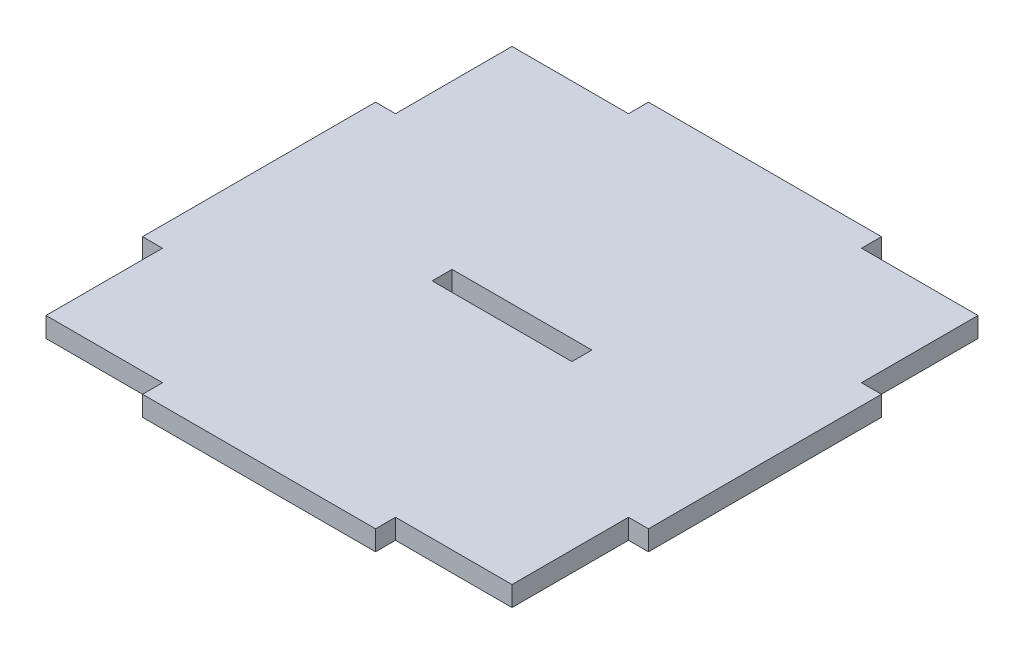
SolidWorks part; units mm, degrees
ref_plane "Front Plane" through (0, 0, 0) normal (0, 0, 1) x (1, 0, 0)
ref_plane "Top Plane" through (0, 0, 0) normal (0, 1, 0) x (1, 0, 0)
ref_plane "Right Plane" through (0, 0, 0) normal (1, 0, 0) x (0, 0, -1)
sketch "Sketch1" plane through (0, 0, 0) normal (0, 1, 0) x (1, 0, 0)
  line L0 (0, 35) -> (0, -35) construction
  line L1 (-35, -35) -> (-17.5, -35)
  line L2 (-35, -35) -> (-35, -17.5)
  line L3 (-35, 35) -> (-17.5, 35)
  line L4 (35, -35) -> (35, -17.5)
  line L5 (-35, -35) -> (35, 35) construction
  line L6 (-35, 35) -> (35, -35) construction
  line L11 (-38, -38) -> (38, 38) construction
  line L12 (-38, 38) -> (38, -38) construction
  line L13 (-35, 0) -> (35, 0) construction
  line L14 (-17.5, 38) -> (-17.5, 35)
  line L15 (-38, 17.5) -> (-35, 17.5)
  line L16 (17.5, 38) -> (17.5, 35)
  line L17 (-38, -17.5) -> (-35, -17.5)
  line L18 (38, 17.5) -> (35, 17.5)
  line L19 (38, -17.5) -> (35, -17.5)
  line L20 (17.5, -38) -> (17.5, -35)
  line L21 (-17.5, -38) -> (-17.5, -35)
  line L22 (-38, -17.5) -> (-38, 17.5)
  line L23 (38, 17.5) -> (38, -17.5)
  line L24 (-17.5, -38) -> (17.5, -38)
  line L25 (-17.5, 38) -> (17.5, 38)
  line L26 (17.5, 35) -> (35, 35)
  line L27 (35, 17.5) -> (35, 35)
  line L28 (17.5, -35) -> (35, -35)
  line L29 (-35, 17.5) -> (-35, 35)
  point P0 (0, 0)
  point P6 (0, 0)
  dimension "D1" = 76
  dimension "D2" = 70
  dimension "D3" = 76
  dimension "D4" = 70
  dimension "D5" = 17.5
  dimension "D6" = 17.5
  dimension "D7" = 3
  dimension "D8" = 3
extrude "Boss-Extrude1" add sketch "Sketch1" along normal blind 3
sketch "Sketch2" plane through (0, 3, 0) normal (0, 1, 0) x (1, 0, 0)
  line L1 (-10.5, -1.5) -> (10.5, -1.5)
  line L2 (-10.5, -1.5) -> (-10.5, 1.5)
  line L3 (-10.5, 1.5) -> (10.5, 1.5)
  line L4 (10.5, -1.5) -> (10.5, 1.5)
  line L5 (-10.5, -1.5) -> (10.5, 1.5) construction
  line L6 (-10.5, 1.5) -> (10.5, -1.5) construction
  point P0 (0, 0)
  dimension "D1" = 21
  dimension "D2" = 3
extrude "Cut-Extrude1" cut sketch "Sketch2" against normal blind 3
